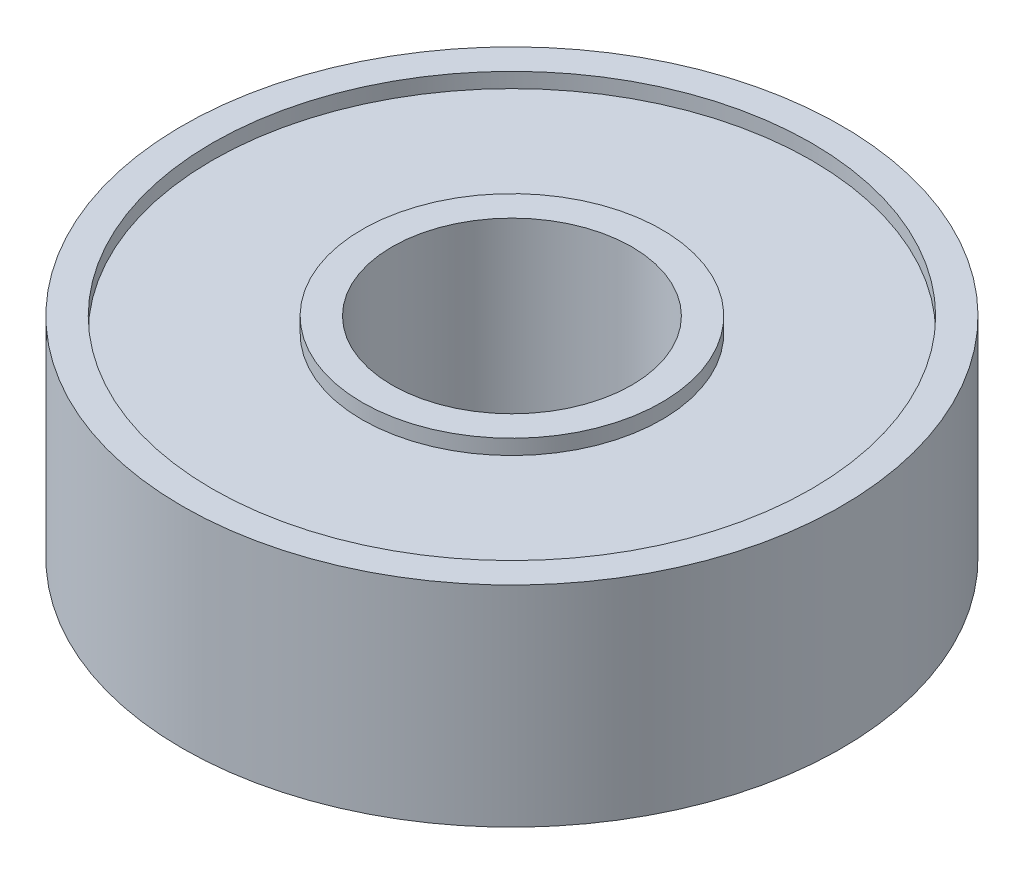
SolidWorks part; units mm, degrees
ref_plane "Front Plane" through (0, 0, 0) normal (0, 0, 1) x (1, 0, 0)
ref_plane "Top Plane" through (0, 0, 0) normal (0, 1, 0) x (1, 0, 0)
ref_plane "Right Plane" through (0, 0, 0) normal (1, 0, 0) x (0, 0, -1)
sketch "Sketch1" plane through (0, 0, 0) normal (0, 1, 0) x (1, 0, 0)
  circle A0 centre (0, 0) radius 11
extrude "Boss-Extrude1" add sketch "Sketch1" along normal blind 7
sketch "Sketch2" plane through (0, 7, 0) normal (0, 1, 0) x (1, 0, 0)
  circle A0 centre (0, 0) radius 4
extrude "Cut-Extrude1" cut sketch "Sketch2" against normal blind 7
sketch "Sketch3" plane through (0, 7, 0) normal (0, 1, 0) x (1, 0, 0)
  circle A0 centre (0, 0) radius 11 construction
  circle A1 centre (0, 0) radius 4 construction
  circle A2 centre (0, 0) radius 11
  circle A3 centre (0, 0) radius 4
  circle A4 centre (0, 0) radius 5
  circle A5 centre (0, 0) radius 10
  dimension "D1" = 1
  dimension "D2" = 1
extrude "Cut-Extrude2" cut sketch "Sketch3" against normal blind 0.5 contours A5 A4
sketch "Sketch4" plane through (0, 0, 0) normal (0, -1, 0) x (1, 0, 0)
  circle A1 centre (0, 0) radius 11
  circle A2 centre (0, 0) radius 11
  circle A3 centre (0, 0) radius 10
  circle A4 centre (0, 0) radius 5
  circle A5 centre (0, 0) radius 5
  dimension "D1" = 0
  dimension "D2" = 1
  dimension "D3" = 1
extrude "Cut-Extrude3" cut sketch "Sketch4" against normal blind 0.5 contours A3 A5
